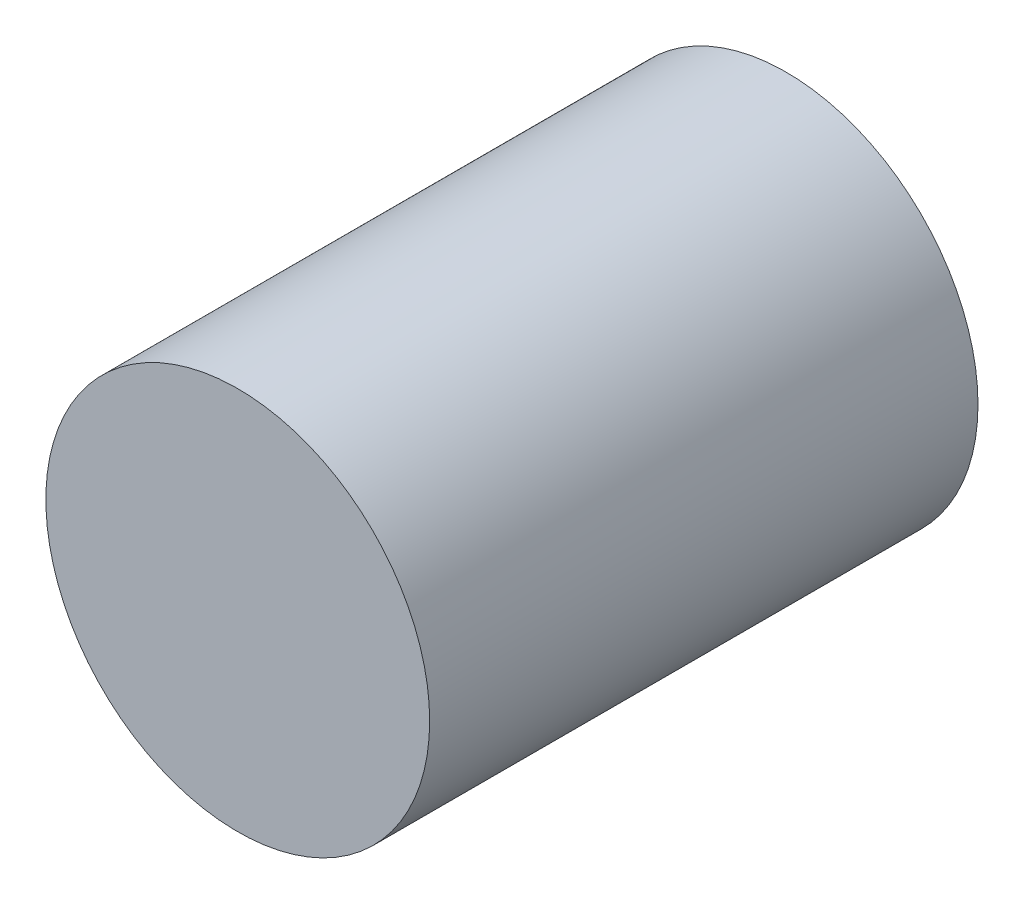
SolidWorks part; units mm, degrees
ref_plane "Front Plane" through (0, 0, 0) normal (0, 0, 1) x (1, 0, 0)
ref_plane "Top Plane" through (0, 0, 0) normal (0, 1, 0) x (1, 0, 0)
ref_plane "Right Plane" through (0, 0, 0) normal (1, 0, 0) x (0, 0, -1)
sketch "Sketch1" plane through (0, 0, 0) normal (0, 0, 1) x (1, 0, 0)
  circle A0 centre (0, 0) radius 1.75
  dimension "D1" = 3.5
extrude "Boss-Extrude1" add sketch "Sketch1" along normal blind 5
